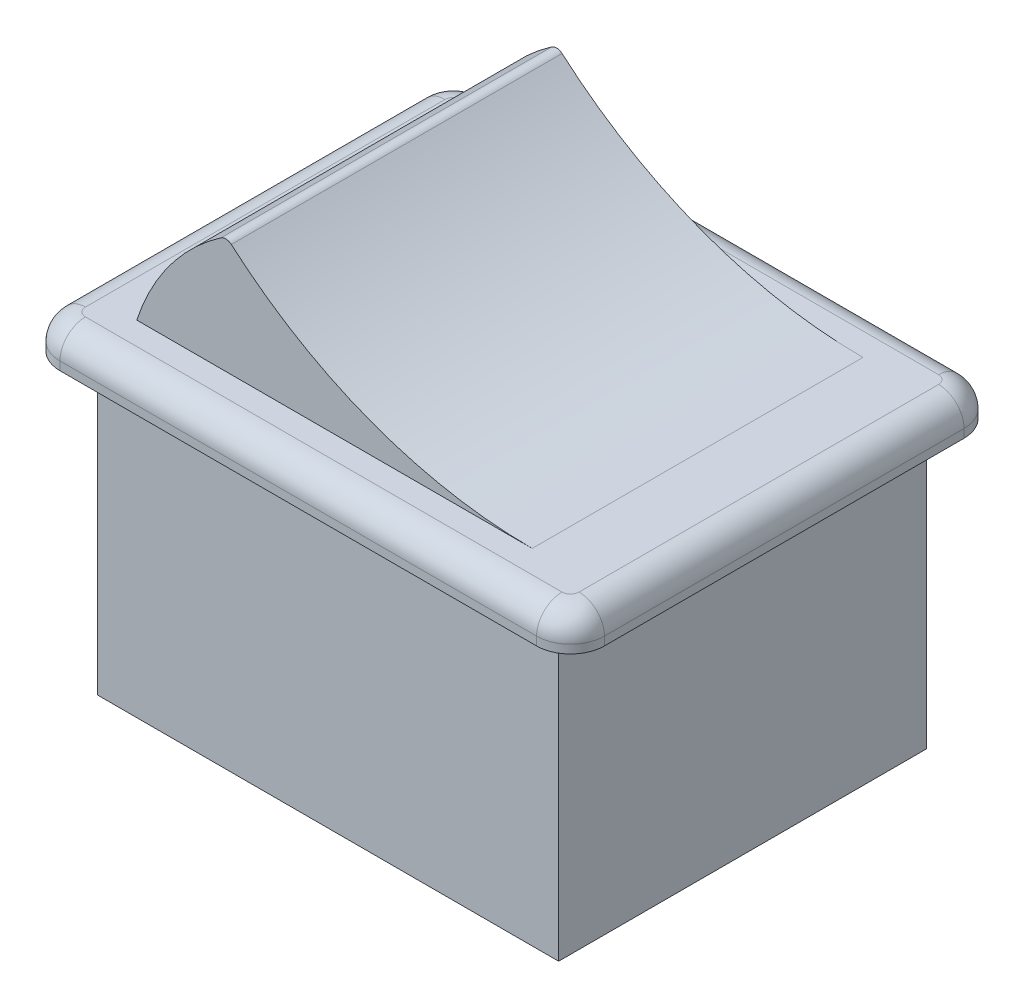
SolidWorks part; units mm, degrees
ref_plane "Front Plane" through (0, 0, 0) normal (0, 0, 1) x (1, 0, 0)
ref_plane "Top Plane" through (0, 0, 0) normal (0, 1, 0) x (1, 0, 0)
ref_plane "Right Plane" through (0, 0, 0) normal (1, 0, 0) x (0, 0, -1)
sketch "Sketch1" plane through (0, 0, 0) normal (0, 1, 0) x (1, 0, 0)
  line L0 (16.05, 12.6) -> (-16.05, -12.6) construction
  line L1 (-14.05, 12.6) -> (14.05, 12.6)
  line L2 (-16.05, 10.6) -> (-16.05, -10.6)
  line L3 (-14.05, -12.6) -> (14.05, -12.6)
  line L4 (16.05, 10.6) -> (16.05, -10.6)
  arc A0 (14.05, 12.6) -> (16.05, 10.6) centre (14.05, 10.6) cw
  arc A1 (14.05, -12.6) -> (16.05, -10.6) centre (14.05, -10.6) ccw
  arc A2 (-16.05, -10.6) -> (-14.05, -12.6) centre (-14.05, -10.6) ccw
  arc A3 (-14.05, 12.6) -> (-16.05, 10.6) centre (-14.05, 10.6) ccw
  point P10 (16.05, -12.6)
  point P16 (-16.05, 12.6)
  dimension "D3" = 2
  dimension "D1" = 32.1
  dimension "D2" = 25.2
extrude "Boss-Extrude1" add sketch "Sketch1" along normal blind 2
fillet "Fillet1" radius 1.5 8 edges at (16.05, 2, 0) (15.4642, 2, 12.0142) (0, 2, 12.6) (-15.4642, 2, 12.0142) (-16.05, 2, 0) (-15.4642, 2, -12.0142) (0, 2, -12.6) (15.4642, 2, -12.0142)
sketch "Sketch3" plane through (0, 0, 0) normal (0, 0, 1) x (1, 0, 0)
  line L0 (-14.05, 2) -> (14.05, 2) construction
  line L1 (-14.05, 0) -> (14.05, 0) construction
  line L2 (-12.3693, 2) -> (10.943, 2)
  arc A0 (-7.4114, 8.6804) -> (-12.3693, 2) centre (0, -2) ccw
  arc A1 (-6.7978, 8.6465) -> (10.943, 2) centre (10.943, 29) ccw
  arc A2 (-6.7978, 8.6465) -> (-7.4114, 8.6804) centre (-7.1264, 8.2696) ccw
  point P12 (-7.0845, 8.9)
  dimension "D2" = 26
  dimension "D4" = 27
  dimension "D5" = 0.5
  dimension "D1" = 2
  dimension "D3" = 6.9
extrude "Boss-Extrude2" add sketch "Sketch3" along normal mid plane 19.5
sketch "Sketch4" plane through (0, 0, 0) normal (0, 0, 1) x (1, 0, 0)
  line L0 (-14.05, 0) -> (14.05, 0) construction
  line L1 (-13.6, 0) -> (13.6, 0)
  line L2 (-13.6, 0) -> (-13.6, -17.2)
  line L3 (-13.6, -17.2) -> (13.6, -17.2)
  line L4 (13.6, 0) -> (13.6, -17.2)
  line L5 (0, 0) -> (0, -17.2) construction
  dimension "D1" = 27.2
  dimension "D2" = 17.2
extrude "Boss-Extrude3" add sketch "Sketch4" along normal mid plane 21.7
